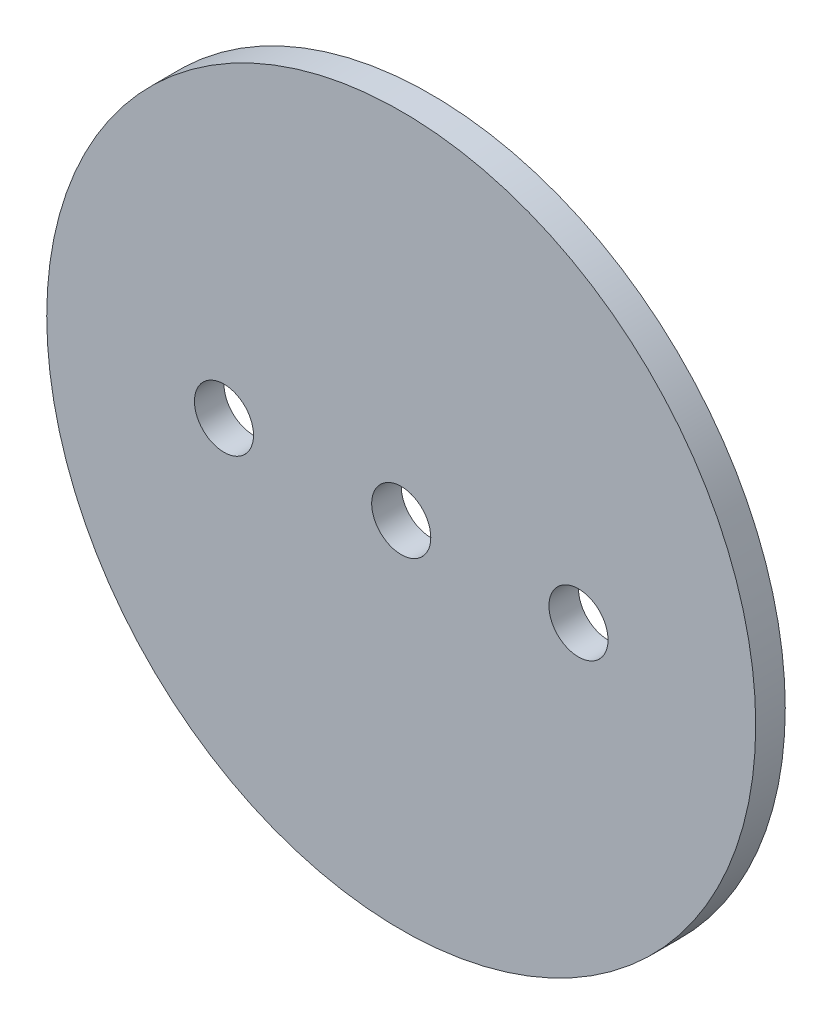
SolidWorks part; units mm, degrees
ref_plane "Front Plane" through (0, 0, 0) normal (0, 0, 1) x (1, 0, 0)
ref_plane "Top Plane" through (0, 0, 0) normal (0, 1, 0) x (1, 0, 0)
ref_plane "Right Plane" through (0, 0, 0) normal (1, 0, 0) x (0, 0, -1)
sketch "Sketch1" plane through (0, 0, 0) normal (0, 0, 1) x (1, 0, 0)
  circle A0 centre (0, 0) radius 38.1
  dimension "D1" = 76.2
extrude "Boss-Extrude1" add sketch "Sketch1" along normal mid plane 3.175
sketch "Sketch2" plane through (0, 0, 1.5875) normal (0, 0, 1) x (1, 0, 0)
  line L0 (-1000, 0) -> (49000, 0) construction
  point P1 (0, 0)
  point P4 (19.05, 0)
  point P5 (-19.05, 0)
  dimension "D1" = 19.05
  dimension "D2" = 38.1
hole_wizard "1/4 (0.25) Diameter Hole1" positions "Sketch2" profile "Sketch3" hole size "1/4" standard "ANSI Inch" end condition through all
sketch "Sketch3" plane through (-19.05, 0, 1.5875) normal (1, 0, 0) x (0, -1, 0)
  line L0 (0, 0) -> (0, 3.175)
  line L1 (0, 3.175) -> (3.175, 3.175)
  line L2 (3.175, 3.175) -> (3.175, 0)
  line L5 (3.175, 0) -> (0, 0)
  line L11 (0, -6.35) -> (0, 107.95) construction
  dimension "Thru Hole Dia." = 6.35
  dimension "Thru Hole Depth" = 3.175
equation "\"AIRFRAME_OD\"= 3.142in"
equation "\"AIRFRAME_ID\"= 3.00in"
equation "\"FLAT_T\"= 0.125in"
equation "\"NOSE_EXP_L\"= 3.5in"
equation "\"NOSE_SHOULDER_L\"= 5in"
equation "\"MAIN_L\"= 30in"
equation "\"RECO_COUP_L\"= 6in"
equation "\"RECO_SWITCH_L\"= 1.5in"
equation "\"DROGUE_L\"= 14in"
equation "\"ATS_FORE_COUP_L\"= 4in"
equation "\"ATS_AFT_COUP_L\"= 2.5in"
equation "\"LOWER_L\"= 16in"
equation "\"FIN_N\"= 4"
equation "\"CR_AFT_X\"= 0.5in"
equation "\"CR_FORE_X\"= 6in"
equation "\"FIN_ROOT\"= 5in"
equation "\"FIN_X\"= 0.75in"
equation "\"MOTOR_OD\"= 2.25in"
equation "\"MOTOR_ID\"= 2.126in"
equation "\"COUPLER_OD\"= 2.998in"
equation "\"COUPLER_ID\"= 2.875in"
equation "\"D1@Sketch1\"=\"AIRFRAME_ID\""
equation "\"D1@Boss-Extrude1\"=\"FLAT_T\""
equation "\"RECO_ROD_X\"= 1.5in"
equation "\"ATS_ROD_X\"= 2in"
equation "\"D1@Sketch2\"=\"RECO_ROD_X\"*0.5"
equation "\"D2@Sketch2\"=\"RECO_ROD_X\""
